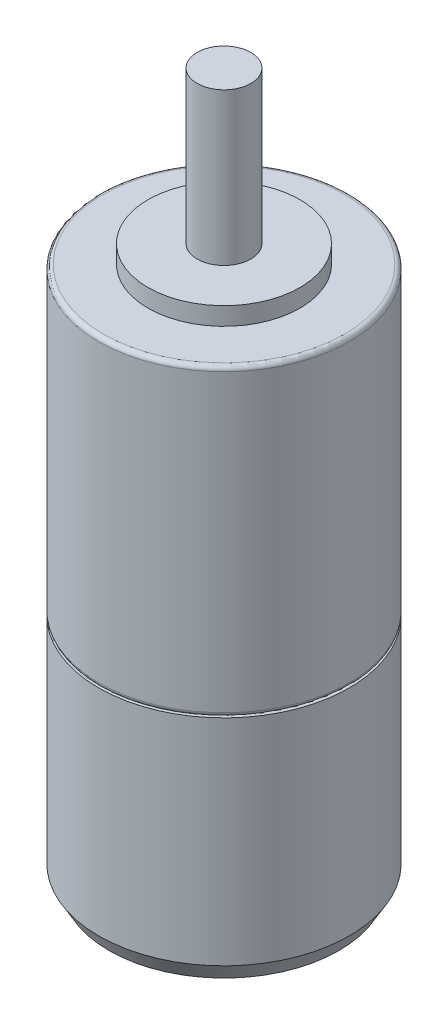
SolidWorks part; units mm, degrees
material "Commercially Pure CP-Ti UNS R50400 (SS)"
ref_plane "Front Plane" through (0, 0, 0) normal (0, 0, 1) x (1, 0, 0)
ref_plane "Top Plane" through (0, 0, 0) normal (0, 1, 0) x (1, 0, 0)
ref_plane "Right Plane" through (0, 0, 0) normal (1, 0, 0) x (0, 0, -1)
sketch "Sketch1" plane through (0, 0, 0) normal (0, 1, 0) x (1, 0, 0)
  circle A0 centre (0, 0) radius 14
  dimension "D1" = 28
extrude "Boss-Extrude1" add sketch "Sketch1" along normal blind 34
sketch "Sketch2" plane through (0, 34, 0) normal (0, 1, 0) x (1, 0, 0)
  circle A0 centre (0, 0) radius 8.5
  dimension "D1" = 17
extrude "Boss-Extrude2" add sketch "Sketch2" along normal blind 2
sketch "Sketch3" plane through (0, 36, 0) normal (0, 1, 0) x (1, 0, 0)
  circle A0 centre (0, 0) radius 3
  dimension "D1" = 6
extrude "Boss-Extrude3" add sketch "Sketch3" along normal blind 17
fillet "Fillet1" radius 0.5 2 edges at (0, 0, 14) (0, 34, 14)
sketch "Sketch5" plane through (0, 0, 0) normal (0, -1, 0) x (1, 0, 0)
  circle A0 centre (0, 0) radius 14
  dimension "D1" = 28
extrude "Boss-Extrude4" add sketch "Sketch5" along normal blind 26
chamfer "Chamfer1" distance 2 angle 30 1 edges at (0, -26, -14)
sketch "Sketch6" plane through (0, -26, 0) normal (0, -1, 0) x (1, 0, 0)
  circle A0 centre (0, 0) radius 6
  dimension "D1" = 12
extrude "Cut-Extrude1" cut sketch "Sketch6" against normal blind 57
